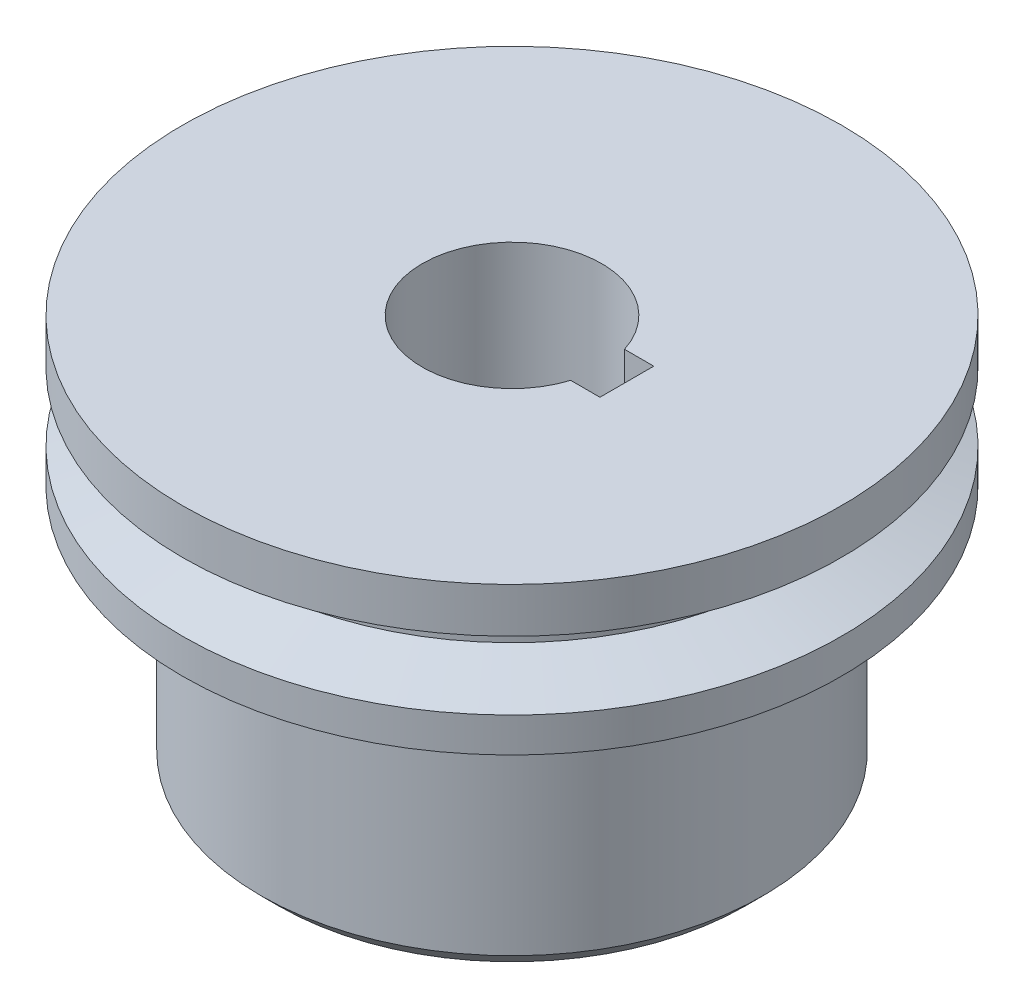
SolidWorks part; units mm, degrees
ref_plane "Front Plane" through (0, 0, 0) normal (0, 0, 1) x (1, 0, 0)
ref_plane "Top Plane" through (0, 0, 0) normal (0, 1, 0) x (1, 0, 0)
ref_plane "Right Plane" through (0, 0, 0) normal (1, 0, 0) x (0, 0, -1)
sketch "Sketch1" plane through (0, 0, 0) normal (0, 1, 0) x (1, 0, 0)
  line L1 (4.7697, -1.5) -> (6.4, -1.5)
  line L2 (4.7697, 1.5) -> (6.4, 1.5)
  line L3 (6.4, 1.5) -> (6.4, -1.5)
  line L4 (0, 0.9083) -> (0, -0.7205) construction
  circle A0 centre (0, 0) radius 14
  arc A1 (4.7697, 1.5) -> (4.7697, -1.5) centre (0, 0) ccw
  dimension "D3" = 6.4
extrude "Boss-Extrude2" add sketch "Sketch1" along normal blind 22 contours A0 | L2 L3 L1 A1
chamfer "Chamfer1" distance 1 angle 45 1 edges at (0, 0, 14)
sketch "Sketch2" plane through (0, 0, 0) normal (1, 0, 0) x (0, 0, -1)
  line L0 (14, 22) -> (18.3628, 22)
  line L2 (18.3628, 22) -> (18.3628, 19.5)
  line L3 (18.3628, 19.5) -> (15, 18.6544)
  line L4 (15, 18.6544) -> (15, 16.812)
  line L5 (15, 16.812) -> (18.3628, 15.6979)
  line L6 (18.3628, 15.6979) -> (18.3628, 13.7698)
  line L7 (18.3628, 13.7698) -> (14, 13.7698)
  line L8 (14, 1) -> (14, 22) construction
  line L9 (14, 13.7698) -> (14, 22)
  line L10 (0, 22) -> (0, 1) construction
  line L11 (0, 22) -> (0, 9.9519) construction
  line L12 (14, 22) -> (-14, 22) construction
  dimension "D1" = 15
  dimension "D2" = 32.444
revolve "Revolve1" add sketch "Sketch2" angle 360 about L11
